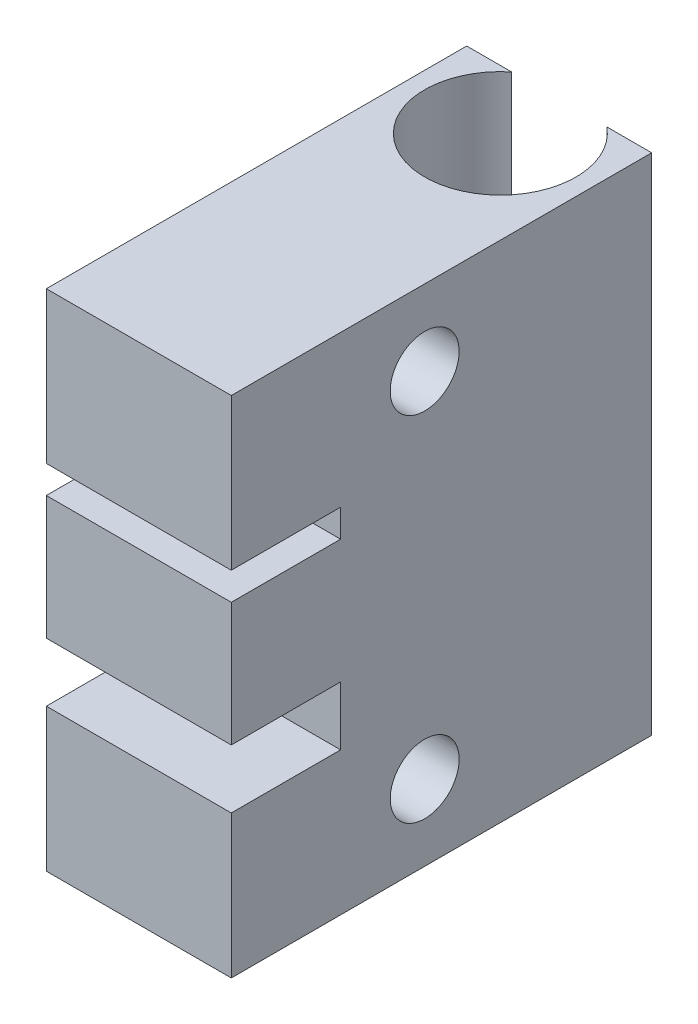
SolidWorks part; units mm, degrees
ref_plane "Front Plane" through (0, 0, 0) normal (0, 0, 1) x (1, 0, 0)
ref_plane "Top Plane" through (0, 0, 0) normal (0, 1, 0) x (1, 0, 0)
ref_plane "Right Plane" through (0, 0, 0) normal (1, 0, 0) x (0, 0, -1)
sketch "Sketch1" plane through (0, 0, 0) normal (0, 1, 0) x (1, 0, 0)
  line L1 (11, 25) -> (-11, 25)
  line L2 (11, 25) -> (11, -25)
  line L3 (11, -25) -> (-11, -25)
  line L4 (-11, 25) -> (-11, -25)
  point P4 (0, 25)
  point P6 (11, 0)
  dimension "D1" = 50
  dimension "D2" = 22
extrude "Boss-Extrude1" add sketch "Sketch1" along normal blind 60
sketch "Sketch2" plane through (11, 0, 0) normal (1, 0, 0) x (0, 0, -1)
  line L0 (-25, 60) -> (25, 60) construction
  line L1 (-25, 0) -> (25, 0) construction
  line L3 (25, 60) -> (25, 0) construction
  circle A0 centre (-2, 51) radius 4.1
  circle A1 centre (-2, 9) radius 4.1
  dimension "D1" = 9
  dimension "D2" = 9
  dimension "D3" = 27
  dimension "D4" = 27
extrude "Cut-Extrude1" cut sketch "Sketch2" against normal through all
sketch "Sketch4" plane through (0, 60, 0) normal (0, 1, 0) x (1, 0, 0)
  line L0 (11, 25) -> (-11, 25) construction
  circle A0 centre (0, 18) radius 9
  dimension "D1" = 7
extrude "Cut-Extrude2" cut sketch "Sketch4" against normal through all
sketch "Sketch5" plane through (0, 0, 25) normal (0, 0, 1) x (1, 0, 0)
  line L0 (-11, 60) -> (-11, 0) construction
  line L1 (-11, 42) -> (11, 42)
  line L2 (-11, 42) -> (-11, 38.7)
  line L3 (-11, 38.7) -> (11, 38.7)
  line L4 (11, 42) -> (11, 38.7)
  line L5 (11, 60) -> (11, 0) construction
  line L6 (-11, 60) -> (11, 60) construction
  line L7 (-11, 24) -> (11, 24)
  line L8 (-11, 24) -> (-11, 17)
  line L9 (-11, 17) -> (11, 17)
  line L10 (11, 24) -> (11, 17)
  line L11 (-11, 0) -> (11, 0) construction
  dimension "D1" = 7
  dimension "D2" = 3.3
  dimension "D3" = 18
  dimension "D4" = 17
extrude "Cut-Extrude3" cut sketch "Sketch5" against normal blind 13
